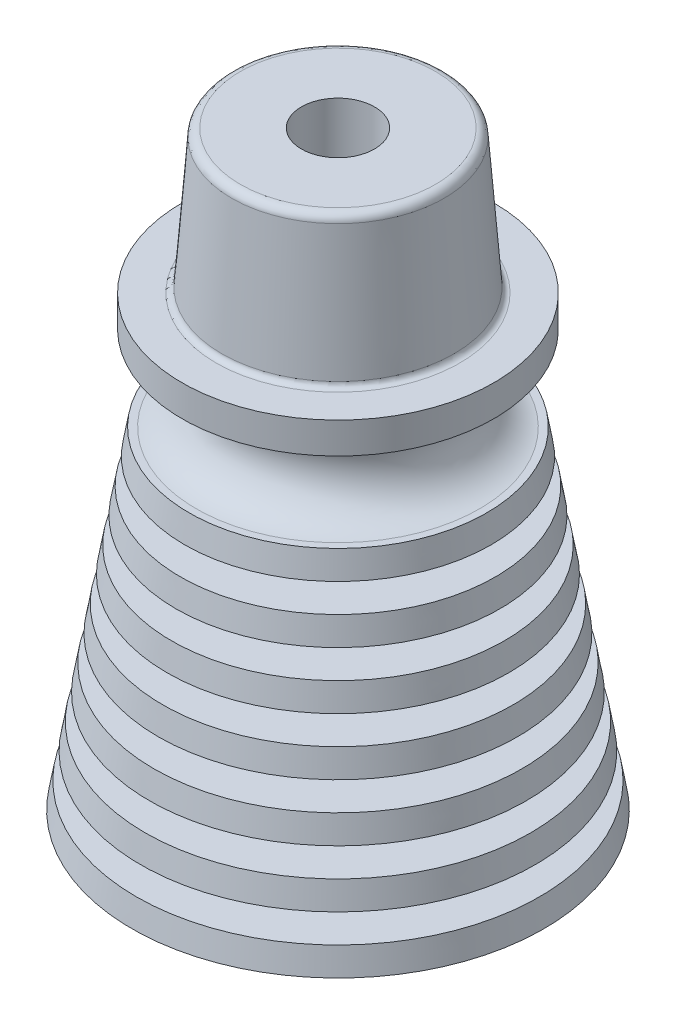
SolidWorks part; units mm, degrees
ref_plane "Front Plane" through (0, 0, 0) normal (0, 0, 1) x (1, 0, 0)
ref_plane "Top Plane" through (0, 0, 0) normal (0, 1, 0) x (1, 0, 0)
ref_plane "Right Plane" through (0, 0, 0) normal (1, 0, 0) x (0, 0, -1)
sketch "Sketch1" plane through (0, 0, 0) normal (0, 0, 1) x (1, 0, 0)
  line L0 (0, 0) -> (0, 105.2466) construction
  line L1 (0, 0) -> (16.8253, 0) construction
  line L2 (2.5273, 14.859) -> (4.191, 0) construction
  line L3 (0, 14.859) -> (9.4545, 14.859) construction
  line L4 (6.6675, 14.859) -> (9.2329, 0) construction
  line L5 (4.572, 14.859) -> (6.2357, 0)
  line L6 (4.5467, 15.0851) -> (6.2104, 0.2261) construction
  line L7 (4.572, 14.859) -> (2.5273, 14.859)
  line L8 (2.5273, 14.859) -> (4.191, 0)
  line L9 (4.191, 0) -> (6.2357, 0)
  circle A0 centre (0, 0) radius 9.2329 construction
  circle A1 centre (0, 14.859) radius 6.6675 construction
  circle A2 centre (0, 0) radius 4.191 construction
  circle A3 centre (0, 14.859) radius 2.5273 construction
  dimension "D1" = 18.4658
  dimension "D3" = 13.335
  dimension "D4" = 8.382
  dimension "D5" = 5.0546
  dimension "D2" = 14.859
  dimension "D6" = 2.032
revolve "Revolve1" add sketch "Sketch1" angle 360 about L0
sketch "Sketch2" plane through (0, 0, 0) normal (0, 0, 1) x (1, 0, 0)
  line L0 (0, 0) -> (16.8253, 0) construction
  line L1 (6.6675, 14.859) -> (9.2329, 0) construction
  line L2 (4.572, 14.859) -> (6.2357, 0) construction
  line L4 (6.2357, 0) -> (9.2329, 0)
  line L5 (9.0356, 1.143) -> (9.2329, 0)
  line L6 (6.1077, 1.143) -> (6.2357, 0)
  line L7 (6.1077, 1.143) -> (9.0356, 1.143)
  line L8 (4.572, 14.859) -> (4.7, 13.716)
  line L9 (6.6675, 14.859) -> (6.8648, 13.716)
  line L10 (5.9797, 2.286) -> (8.8382, 2.286)
  line L11 (5.8518, 3.429) -> (8.6409, 3.429)
  line L12 (5.7238, 4.572) -> (8.4435, 4.572)
  line L13 (5.5958, 5.715) -> (8.2462, 5.715)
  line L14 (5.4678, 6.858) -> (8.0489, 6.858)
  line L15 (5.3399, 8.001) -> (7.8515, 8.001)
  line L16 (8.2462, 5.715) -> (8.4435, 4.572)
  line L17 (5.5958, 5.715) -> (5.7238, 4.572)
  line L18 (5.8518, 3.429) -> (5.9797, 2.286)
  line L19 (8.6409, 3.429) -> (8.8382, 2.286)
  line L20 (5.2119, 9.144) -> (7.6542, 9.144)
  line L21 (5.0839, 10.287) -> (7.4569, 10.287)
  line L22 (4.9559, 11.43) -> (7.2595, 11.43)
  line L23 (4.828, 12.573) -> (7.0622, 12.573)
  line L24 (7.8515, 8.001) -> (8.0489, 6.858)
  line L25 (5.3399, 8.001) -> (5.4678, 6.858)
  line L26 (7.4569, 10.287) -> (7.6542, 9.144)
  line L27 (5.0839, 10.287) -> (5.2119, 9.144)
  line L28 (4.572, 14.859) -> (6.6675, 14.859)
  line L29 (4.7, 13.716) -> (6.8648, 13.716)
  line L30 (4.828, 12.573) -> (4.9559, 11.43)
  line L31 (7.0622, 12.573) -> (7.2595, 11.43)
  dimension "D1" = 1.143
  dimension "D2" = 1.143
  dimension "D3" = 2.286
  dimension "D4" = 1.143
  dimension "D5" = 2.286
  dimension "D6" = 1.143
  dimension "D7" = 2.286
  dimension "D8" = 1.143
  dimension "D9" = 2.286
  dimension "D10" = 2.286
  dimension "D11" = 1.143
  dimension "D12" = 1.143
revolve "Revolve2" add sketch "Sketch2" angle 360 about L0
sketch "Sketch3" plane through (0, 0, 0) normal (0, 0, 1) x (1, 0, 0)
  line L0 (6.6675, 14.859) -> (-6.6675, 14.859) construction
  line L1 (6.35, 14.859) -> (0, 14.859)
  line L2 (0, 0) -> (0, 26.3541) construction
  line L4 (6.35, 18.669) -> (6.985, 18.669)
  line L5 (0, 20.066) -> (6.985, 20.066)
  line L6 (6.985, 20.066) -> (6.985, 18.669)
  line L7 (-9.2329, 0) -> (9.2329, 0) construction
  line L8 (6.35, 18.669) -> (6.35, 14.859) construction
  line L9 (0, 20.066) -> (0, 14.859)
  arc A0 (6.35, 18.669) -> (6.35, 14.859) centre (6.6088, 16.764) ccw
  dimension "D5" = 9.3726
  dimension "D1" = 1.397
  dimension "D2" = 20.066
  dimension "D3" = 13.97
  dimension "D4" = 0.635
revolve "Revolve3" add sketch "Sketch3" angle 360 about L2
sketch "Sketch4" plane through (0, 0, 0) normal (0, 0, 1) x (1, 0, 0)
  line L0 (0, 0) -> (0, 32.0807) construction
  line L1 (6.985, 20.066) -> (-6.985, 20.066) construction
  line L2 (5.2197, 20.066) -> (0, 20.066)
  line L3 (0, 29.2608) -> (4.5212, 29.2608) construction
  line L4 (4.7335, 26.4668) -> (5.2197, 20.066)
  line L5 (0, 20.066) -> (0, 26.4668)
  line L6 (-9.2329, 0) -> (9.2329, 0) construction
  line L7 (0, 26.4668) -> (4.7335, 26.4668)
  line L8 (4.7335, 26.4668) -> (4.5212, 29.2608) construction
  dimension "D1" = 9.0424
  dimension "D2" = 10.4394
  dimension "D3" = 29.2608
  dimension "D4" = 26.4668
revolve "Revolve4" add sketch "Sketch4" angle 360 about L0
sketch "Sketch5" plane through (0, 26.4668, 0) normal (0, 1, 0) x (1, 0, 0)
  circle A0 centre (0, 0) radius 1.6383
  dimension "D1" = 3.2766
extrude "Cut-Extrude1" cut sketch "Sketch5" against normal through all
fillet "Fillet1" radius 0.381 1 edges at (0, 26.4668, -4.7335)
fillet "Fillet2" radius 0.254 1 edges at (0, 20.066, 5.2197)
ref_plane "Plane1" through (0, 16.764, 0) normal (0, -1, 0) x (-1, 0, 0)
sketch "Sketch6" plane through (0, 16.764, 0) normal (0, -1, 0) x (-1, 0, 0)
  circle A0 centre (0, 0) radius 7.62 construction
  dimension "D1" = 15.24
